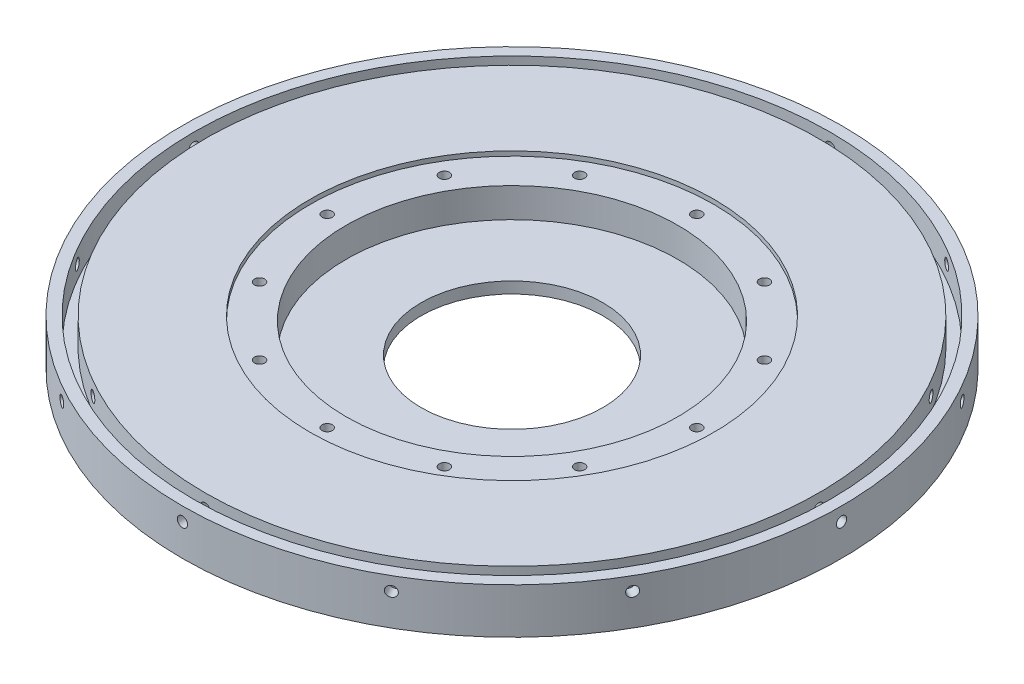
SolidWorks part; units mm, degrees
material "6061-T6 (SS)"
ref_plane "Front Plane" through (0, 0, 0) normal (0, 0, 1) x (1, 0, 0)
ref_plane "Top Plane" through (0, 0, 0) normal (0, 1, 0) x (1, 0, 0)
ref_plane "Right Plane" through (0, 0, 0) normal (1, 0, 0) x (0, 0, -1)
sketch "Sketch1" plane through (0, 0, 0) normal (0, 1, 0) x (1, 0, 0)
  line L5 (0, 0) -> (127.635, 0)
  line L6 (0, 0) -> (0, 127.635)
  line L7 (0, 127.635) -> (127.635, 127.635)
  line L8 (127.635, 0) -> (127.635, 127.635)
  dimension "D1" = 127.635
  dimension "D2" = 127.635
extrude "Boss-Extrude1" add sketch "Sketch1" along normal blind 9.525 contours L5 L8 L7 L6
sketch "Sketch13" plane through (0, 9.525, 0) normal (0, 1, 0) x (1, 0, 0)
  circle A0 centre (63.8175, 63.8175) radius 92.075
  dimension "D1" = 184.15
extrude "Boss-Extrude2" add sketch "Sketch13" against normal blind 12.7 contours A0
sketch "Sketch6" [suppressed] plane through (127.635, 0, 0) normal (1, 0, 0) x (0, 0, -1)
  circle A0 centre (4.7625, 4.7625) radius 1.3526
  dimension "D1" = 2.7051
extrude "6-32 hole1" [suppressed] cut sketch "Sketch6" against normal blind 12.7
sketch "Sketch7" [suppressed] plane through (0, 0, -127.635) normal (0, 0, -1) x (-1, 0, 0)
  circle A0 centre (-122.8725, 4.7625) radius 1.3525
  dimension "D1" = 2.7051
sketch "Sketch8" [suppressed] plane through (0, 0, 0) normal (-1, 0, 0) x (0, 0, 1)
  circle A0 centre (-122.8725, 4.7625) radius 1.3525
  dimension "D1" = 2.7051
sketch "Sketch9" [suppressed] plane through (0, 0, 0) normal (0, 0, 1) x (1, 0, 0)
  circle A0 centre (4.7625, 4.7625) radius 1.3526
  dimension "D1" = 2.7051
sketch "Sketch5" plane through (0, 9.525, 0) normal (0, 1, 0) x (1, 0, 0)
  circle A0 centre (63.8175, 63.8175) radius 46.355
  circle A1 centre (63.8175, 63.8175) radius 92.075 construction
  dimension "D1" = 92.71
extrude "Cut-Extrude1" cut sketch "Sketch5" against normal blind 9.525
sketch "Sketch11" plane through (0, 9.525, 0) normal (0, 1, 0) x (1, 0, 0)
  line L0 (63.8175, 63.8175) -> (63.8175, 115.443) construction
  circle A0 centre (63.8175, 115.443) radius 1.4351
  dimension "D2" = 2.8702
  dimension "D1" = 51.6255
extrude "Cut-Extrude3" cut sketch "Sketch11" against normal through all contours A0
pattern_circular "CirPattern1" count 12 over 360 about axis through (63.8175, 0, -63.8175) along (0, 1, 0) of "Cut-Extrude3"
sketch "Sketch12" plane through (0, 9.525, 0) normal (0, 1, 0) x (1, 0, 0)
  circle A0 centre (63.8175, 63.8175) radius 56.4198
  dimension "D1" = 112.8395
extrude "Cut-Extrude4" cut sketch "Sketch12" against normal blind 1.27
sketch "Sketch15" plane through (0, 9.525, 0) normal (0, 1, 0) x (1, 0, 0)
  line L0 (63.8175, 63.8175) -> (-28.2575, 63.8175) construction
  line L1 (0, -39.1057) -> (0, 39.1057) construction
  line L2 (-20.0025, 63.8175) -> (-25.0825, 63.8175)
  line L3 (-8.7458, 105.7742) -> (-13.2051, 108.2104)
  line L4 (-8.7458, 105.7742) -> (-20.0025, 63.8175) construction
  circle A0 centre (63.8175, 63.8175) radius 56.4198 construction
  arc A1 (-20.0025, 63.8175) -> (-8.7458, 105.7742) centre (63.8175, 63.8175) cw
  arc A2 (-25.0825, 63.8175) -> (-13.2051, 108.2104) centre (63.8175, 63.8175) cw
  circle A3 centre (63.8175, 63.8175) radius 92.075 construction
  point P0 (63.8175, 63.8175)
  point P11 (-14.3741, 84.7959)
  dimension "D1" = 46.482
  dimension "D2" = 88.9
  dimension "D3" = 83.82
  dimension "D4" = 43.942
sketch "Sketch16" plane through (0, 9.525, 0) normal (0, 1, 0) x (1, 0, 0)
  circle A0 centre (63.8175, 63.8175) radius 88.9
  circle A1 centre (63.8175, 63.8175) radius 85.725
  dimension "D1" = 177.8
  dimension "D2" = 171.45
extrude "Cut-Extrude5" cut sketch "Sketch16" against normal blind 7.62
sketch "Sketch18" plane through (0, 8.255, 0) normal (0, 1, 0) x (1, 0, 0)
  line L0 (63.8175, 185.7252) -> (63.8175, -48.6103) construction
ref_plane "Plane1" through (63.8175, 0, 0) normal (-1, 0, 0) x (0, 0, 1)
ref_plane "Plane2" through (0, 0, 28.2575) normal (0, 0, 1) x (1, 0, 0)
sketch "Sketch17" plane through (0, 0, 28.2575) normal (0, 0, 1) x (1, 0, 0)
  line L0 (63.8175, 103.0287) -> (63.8175, -103.0287) construction
  line L1 (155.8925, 9.525) -> (-28.2575, 9.525) construction
  circle A0 centre (63.8175, 5.715) radius 1.4351
  dimension "D1" = 2.8702
  dimension "D2" = 3.81
extrude "Cut-Extrude6" cut sketch "Sketch17" against normal blind 15.24
pattern_circular "CirPattern2" count 12 over 360 about axis through (63.8175, 0, -63.8175) along (0, 1, 0) of "Cut-Extrude6"
sketch "Sketch19" plane through (0, -3.175, 0) normal (0, -1, 0) x (1, 0, 0)
  circle A0 centre (63.8175, -63.8175) radius 25.4
  dimension "D1" = 50.8
extrude "Cut-Extrude7" cut sketch "Sketch19" against normal blind 87.63
